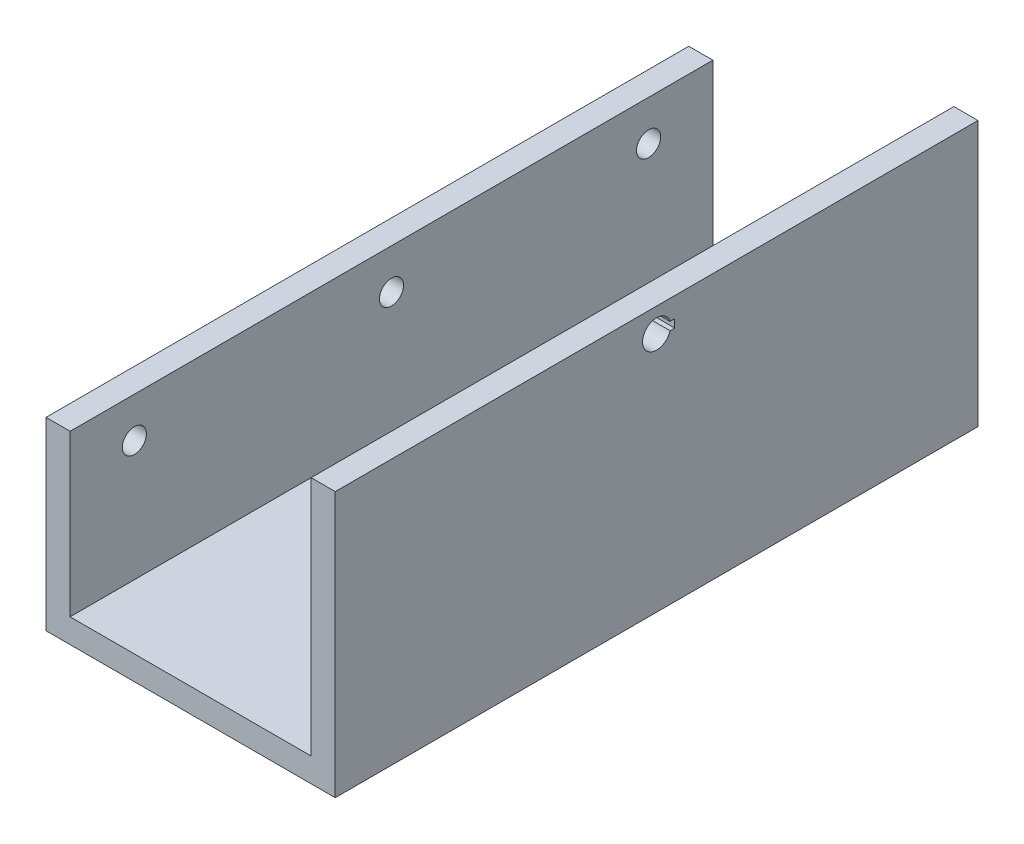
SolidWorks part; units mm, degrees
ref_plane "Front Plane" through (0, 0, 0) normal (0, 0, 1) x (1, 0, 0)
ref_plane "Top Plane" through (0, 0, 0) normal (0, 1, 0) x (1, 0, 0)
ref_plane "Right Plane" through (0, 0, 0) normal (1, 0, 0) x (0, 0, -1)
sketch "Sketch2" plane through (0, 0, 0) normal (0, 0, 1) x (1, 0, 0)
  line L1 (-30, 0) -> (-30, -30)
  line L2 (-30, -30) -> (0, -30)
  line L3 (0, -30) -> (0, 0)
  line L4 (-30, 0) -> (0, 0)
  line L5 (-30, -2.5) -> (0, -2.5) construction
  circle A1 centre (-15, -2.5) radius 1.75
  point P9 (-15, -2.4549)
  point P10 (-15.268, -3.7246)
  dimension "D1" = 3.5
  dimension "D3" = 30
  dimension "D2" = 30
  dimension "D4" = 2.5
extrude "Boss-Extrude1" add sketch "Sketch2" along normal blind 2
sketch "Sketch3" plane through (0, 0, 2) normal (0, 0, 1) x (1, 0, 0)
  line L0 (0, -30) -> (0, 0) construction
  line L1 (-30, -30) -> (0, -30)
  line L2 (-30, -30) -> (-30, -27)
  line L3 (-30, -27) -> (0, -27)
  line L4 (0, -30) -> (0, -27)
  dimension "D1" = 3
extrude "Boss-Extrude2" add sketch "Sketch3" along normal blind 76
ref_plane "Plane1" through (0, 0, 40) normal (0, 0, 1) x (1, 0, 0)
mirror "Mirror1" about plane through (0, 0, 40) normal (0, 0, 1) of "Boss-Extrude1"
extrude "Cut-Extrude1" cut sketch "Sketch7" against normal blind 3
sketch "Sketch7" plane through (-25.653, -30, -8.7727) normal (0, -1, 0) x (1, 0, 0)
  circle A0 centre (10.653, 28.3027) radius 4
sketch "Sketch8" plane through (0, 0, 0) normal (0, 1, 0) x (1, 0, 0)
  line L0 (-30, -80) -> (0, -80) construction
  line L1 (0, -80) -> (0, -78) construction
  line L2 (0, -78) -> (-30, -78) construction
  line L3 (-30, -78) -> (-30, -80) construction
  line L4 (0, 0) -> (-30, 0) construction
  line L5 (-30, 0) -> (-30, -2) construction
  line L6 (-30, -2) -> (0, -2) construction
  line L7 (0, -2) -> (0, 0) construction
  line L8 (-30, -80) -> (0, -80)
  line L9 (0, -80) -> (0, -78)
  line L10 (0, -78) -> (-30, -78)
  line L11 (-30, -78) -> (-30, -80)
  line L12 (0, 0) -> (-30, 0)
  line L13 (-30, 0) -> (-30, -2)
  line L14 (-30, -2) -> (0, -2)
  line L15 (0, -2) -> (0, 0)
extrude "Cut-Extrude2" cut sketch "Sketch8" against normal up to surface (27 mm away) up to face at (-11, -27, 19.53)
sketch "Sketch9" plane through (0, -30, 0) normal (0, -1, 0) x (1, 0, 0)
  line L1 (0, 80) -> (3, 80)
  line L2 (0, 80) -> (0, 0)
  line L3 (0, 0) -> (3, 0)
  line L4 (3, 80) -> (3, 0)
  line L5 (-30, 80) -> (-33, 80)
  line L6 (-30, 80) -> (-30, 0)
  line L7 (-30, 0) -> (-33, 0)
  line L8 (-33, 80) -> (-33, 0)
  dimension "D1" = 80
  dimension "D2" = 3
  dimension "D3" = 3
  dimension "D4" = 80
extrude "Boss-Extrude3" add sketch "Sketch9" against normal blind 33
sketch "Sketch10" plane through (-33, 0, 0) normal (-1, 0, 0) x (0, 0, 1)
  line L0 (0, 0) -> (80, 0) construction
  line L1 (80, 3) -> (80, -30) construction
  circle A0 centre (40, 0) radius 1.75
  dimension "D1" = 3.5
extrude "Cut-Extrude3" cut sketch "Sketch10" against normal through all
extrude "Cut-Extrude4" cut sketch "Sketch11" against normal blind 50
sketch "Sketch11" plane through (-33, -23.4689, -8.7727) normal (-1, 0, 0) x (0, 0, 1)
  line L3 (47.0956, 22.9689) -> (46.5227, 22.9689)
  line L4 (46.5227, 22.9689) -> (46.5227, 23.9689)
  line L5 (46.5227, 23.9689) -> (47.0956, 23.9689)
  arc A1 (47.0956, 22.9689) -> (47.0956, 23.9689) centre (48.7727, 23.4689) ccw
sketch "Sketch12" plane through (-33, 0, 0) normal (-1, 0, 0) x (0, 0, 1)
  line L0 (80, 3) -> (80, -30) construction
  line L1 (0, 3) -> (80, 3)
  line L2 (0, 3) -> (0, -7)
  line L3 (0, -7) -> (80, -7)
  line L4 (80, 3) -> (80, -7)
  dimension "D1" = 10
extrude "Cut-Extrude5" cut sketch "Sketch12" against normal up to next
extrude "Cut-Extrude6" cut sketch "Sketch13" against normal blind 6
sketch "Sketch13" plane through (-36, -23.4689, -8.7727) normal (-1, 0, 0) x (0, 0, 1)
  line L0 (8.7727, 11.4689) -> (88.7727, 11.4689) construction
  circle A0 centre (16.7727, 11.4689) radius 1.5
  circle A1 centre (48.7727, 11.4689) radius 1.5
  circle A2 centre (80.7727, 11.4689) radius 1.5
  point P13 (48.7727, 11.4689)
